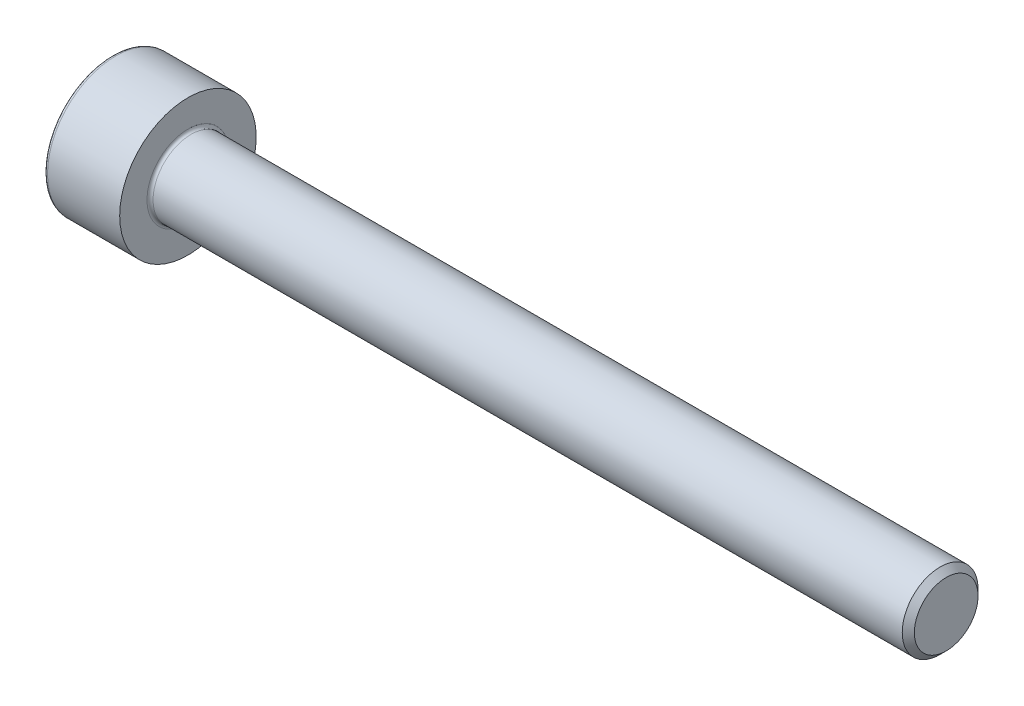
SolidWorks part; units mm, degrees
material "AISI Тип A2 Инструментальная сталь"
ref_plane "Front Plane" through (0, 0, 0) normal (0, 0, 1) x (1, 0, 0)
ref_plane "Top Plane" through (0, 0, 0) normal (0, 1, 0) x (1, 0, 0)
ref_plane "Right Plane" through (0, 0, 0) normal (1, 0, 0) x (0, 0, -1)
sketch "Sketch1" plane through (0, 0, 0) normal (0, 0, 1) x (1, 0, 0)
  line L0 (0, 0) -> (0, 2.25)
  line L1 (0, 2.25) -> (2.5, 2.25)
  line L2 (2.5, 2.25) -> (2.5, 0)
  line L3 (0, 0) -> (4.2799, 0) construction
  line L4 (2.5, 0) -> (27.5, 0)
  line L5 (27.5, 0) -> (27.5, 1.25)
  line L6 (27.5, 1.25) -> (2.5, 1.25)
  dimension "D1" = 25
  dimension "D2" = 2.5
  dimension "D3" = 2.25
  dimension "D4" = 1.25
revolve "Revolve1" add sketch "Sketch1" angle 360 about L3
fillet "Fillet1" radius 0.1 1 edges at (2.5, 0, 1.25)
fillet "Fillet2" radius 0.12 1 edges at (0, 0, 2.25)
chamfer "Chamfer1" distance 0.2 angle 45 1 edges at (27.5, 0, 1.25)
sketch "Sketch2" plane through (0, 0, 0) normal (-1, 0, 0) x (0, 0, 1)
  line L1 (0, 1.1547) -> (-1, 0.5774)
  line L2 (-1, 0.5774) -> (-1, -0.5774)
  line L3 (-1, -0.5774) -> (0, -1.1547)
  line L4 (0, -1.1547) -> (1, -0.5774)
  line L5 (1, -0.5774) -> (1, 0.5774)
  line L6 (1, 0.5774) -> (0, 1.1547)
  circle A0 centre (0, 0) radius 1 construction
  dimension "D1" = 2
extrude "Extrude1" cut sketch "Sketch2" against normal blind 1.1
